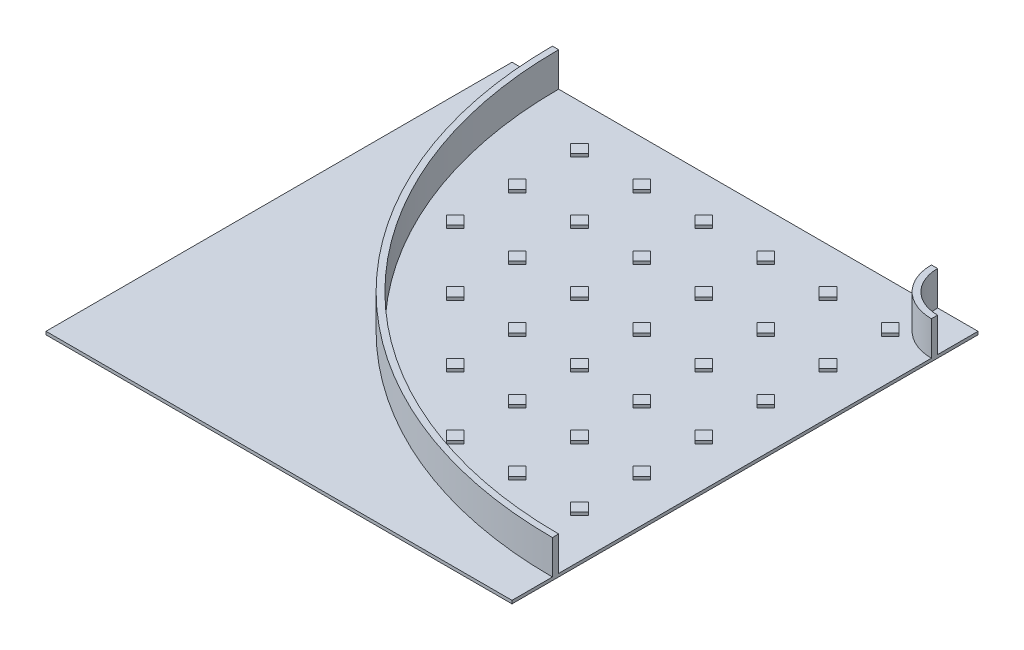
SolidWorks part; units mm, degrees
ref_plane "Front Plane" through (0, 0, 0) normal (0, 0, 1) x (1, 0, 0)
ref_plane "Top Plane" through (0, 0, 0) normal (0, 1, 0) x (1, 0, 0)
ref_plane "Right Plane" through (0, 0, 0) normal (1, 0, 0) x (0, 0, -1)
sketch "Sketch2" plane through (0, 0, 0) normal (0, 1, 0) x (1, 0, 0)
  line L1 (-750, 750) -> (750, 750)
  line L2 (-750, 750) -> (-750, -750)
  line L3 (-750, -750) -> (750, -750)
  line L4 (750, 750) -> (750, -750)
  line L5 (-750, 750) -> (750, -750) construction
  line L6 (-750, -750) -> (750, 750) construction
  point P0 (0, 0)
  dimension "D1" = 1500
  dimension "D2" = 1500
extrude "Boss-Extrude1" add sketch "Sketch2" along normal blind 10
sketch "Sketch3" plane through (0, 10, 0) normal (0, 1, 0) x (1, 0, 0)
  line L0 (620, 750) -> (620, -750) construction
  line L1 (750, 750) -> (-750, 750) construction
  line L2 (-750, -750) -> (750, -750) construction
  line L3 (600, 750) -> (600, -750) construction
  line L4 (750, -750) -> (750, 750) construction
  line L5 (-750, -600) -> (750, -600) construction
  line L6 (-750, 750) -> (-750, -750) construction
  line L7 (-750, -620) -> (750, -620) construction
  line L8 (-750, 0) -> (750, 0) construction
  line L9 (0, 750) -> (0, -750) construction
  line L10 (-750, 620) -> (750, 620) construction
  line L11 (-750, 600) -> (750, 600) construction
  line L12 (-620, 750) -> (-620, -750) construction
  line L13 (-600, 750) -> (-600, -750) construction
  circle A0 centre (750, 750) radius 150
  circle A1 centre (750, 750) radius 1350
  circle A2 centre (750, 750) radius 130
  circle A3 centre (750, 750) radius 1370
  line M3 (750, -750) -> (750, 750)
  line M4 (750, 750) -> (-750, 750)
  dimension "D6" = 150
  dimension "D5" = 20
  dimension "D7" = 20
  dimension "D8" = 150
extrude "Boss-Extrude2" add sketch "Sketch3" along normal blind 110 contours A3 A1 M4 M3 | A2 A0 M4 M3
sketch "Sketch4" plane through (0, 10, 0) normal (0, 1, 0) x (1, 0, 0)
  line L0 (-391.4214, 636.8629) -> (-419.7056, 608.5786)
  line L1 (-391.4214, 636.8629) -> (-363.1371, 608.5786)
  line L2 (-419.7056, 608.5786) -> (-391.4214, 580.2944)
  line L3 (-363.1371, 608.5786) -> (-391.4214, 580.2944)
  line L4 (-391.4214, 636.8629) -> (-391.4214, 580.2944) construction
  line L5 (-419.7056, 608.5786) -> (-363.1371, 608.5786) construction
  line L6 (-191.4214, 636.8629) -> (-219.7056, 608.5786)
  line L7 (-191.4214, 636.8629) -> (-163.1371, 608.5786)
  line L8 (-219.7056, 608.5786) -> (-191.4214, 580.2944)
  line L9 (-163.1371, 608.5786) -> (-191.4214, 580.2944)
  line L10 (-191.4214, 636.8629) -> (-191.4214, 580.2944) construction
  line L11 (-219.7056, 608.5786) -> (-163.1371, 608.5786) construction
  line L12 (8.5786, 636.8629) -> (-19.7056, 608.5786)
  line L13 (8.5786, 636.8629) -> (36.8629, 608.5786)
  line L14 (-19.7056, 608.5786) -> (8.5786, 580.2944)
  line L15 (36.8629, 608.5786) -> (8.5786, 580.2944)
  line L16 (8.5786, 636.8629) -> (8.5786, 580.2944) construction
  line L17 (-19.7056, 608.5786) -> (36.8629, 608.5786) construction
  line L18 (208.5786, 636.8629) -> (180.2944, 608.5786)
  line L19 (208.5786, 636.8629) -> (236.8629, 608.5786)
  line L20 (180.2944, 608.5786) -> (208.5786, 580.2944)
  line L21 (236.8629, 608.5786) -> (208.5786, 580.2944)
  line L22 (208.5786, 636.8629) -> (208.5786, 580.2944) construction
  line L23 (180.2944, 608.5786) -> (236.8629, 608.5786) construction
  line L24 (408.5786, 636.8629) -> (380.2944, 608.5786)
  line L25 (408.5786, 636.8629) -> (436.8629, 608.5786)
  line L26 (380.2944, 608.5786) -> (408.5786, 580.2944)
  line L27 (436.8629, 608.5786) -> (408.5786, 580.2944)
  line L28 (408.5786, 636.8629) -> (408.5786, 580.2944) construction
  line L29 (380.2944, 608.5786) -> (436.8629, 608.5786) construction
  line L30 (-191.4214, 436.8629) -> (-219.7056, 408.5786)
  line L31 (-191.4214, 436.8629) -> (-163.1371, 408.5786)
  line L32 (-219.7056, 408.5786) -> (-191.4214, 380.2944)
  line L33 (-163.1371, 408.5786) -> (-191.4214, 380.2944)
  line L34 (-191.4214, 436.8629) -> (-191.4214, 380.2944) construction
  line L35 (-219.7056, 408.5786) -> (-163.1371, 408.5786) construction
  line L36 (8.5786, 436.8629) -> (-19.7056, 408.5786)
  line L37 (8.5786, 436.8629) -> (36.8629, 408.5786)
  line L38 (-19.7056, 408.5786) -> (8.5786, 380.2944)
  line L39 (36.8629, 408.5786) -> (8.5786, 380.2944)
  line L40 (8.5786, 436.8629) -> (8.5786, 380.2944) construction
  line L41 (-19.7056, 408.5786) -> (36.8629, 408.5786) construction
  line L42 (208.5786, 436.8629) -> (180.2944, 408.5786)
  line L43 (208.5786, 436.8629) -> (236.8629, 408.5786)
  line L44 (180.2944, 408.5786) -> (208.5786, 380.2944)
  line L45 (236.8629, 408.5786) -> (208.5786, 380.2944)
  line L46 (208.5786, 436.8629) -> (208.5786, 380.2944) construction
  line L47 (180.2944, 408.5786) -> (236.8629, 408.5786) construction
  line L48 (408.5786, 436.8629) -> (380.2944, 408.5786)
  line L49 (408.5786, 436.8629) -> (436.8629, 408.5786)
  line L50 (380.2944, 408.5786) -> (408.5786, 380.2944)
  line L51 (436.8629, 408.5786) -> (408.5786, 380.2944)
  line L52 (408.5786, 436.8629) -> (408.5786, 380.2944) construction
  line L53 (380.2944, 408.5786) -> (436.8629, 408.5786) construction
  line L54 (-191.4214, 236.8629) -> (-219.7056, 208.5786)
  line L55 (-191.4214, 236.8629) -> (-163.1371, 208.5786)
  line L56 (-219.7056, 208.5786) -> (-191.4214, 180.2944)
  line L57 (-163.1371, 208.5786) -> (-191.4214, 180.2944)
  line L58 (-191.4214, 236.8629) -> (-191.4214, 180.2944) construction
  line L59 (-219.7056, 208.5786) -> (-163.1371, 208.5786) construction
  line L60 (8.5786, 236.8629) -> (-19.7056, 208.5786)
  line L61 (8.5786, 236.8629) -> (36.8629, 208.5786)
  line L62 (-19.7056, 208.5786) -> (8.5786, 180.2944)
  line L63 (36.8629, 208.5786) -> (8.5786, 180.2944)
  line L64 (8.5786, 236.8629) -> (8.5786, 180.2944) construction
  line L65 (-19.7056, 208.5786) -> (36.8629, 208.5786) construction
  line L66 (208.5786, 236.8629) -> (180.2944, 208.5786)
  line L67 (208.5786, 236.8629) -> (236.8629, 208.5786)
  line L68 (180.2944, 208.5786) -> (208.5786, 180.2944)
  line L69 (236.8629, 208.5786) -> (208.5786, 180.2944)
  line L70 (208.5786, 236.8629) -> (208.5786, 180.2944) construction
  line L71 (180.2944, 208.5786) -> (236.8629, 208.5786) construction
  line L72 (408.5786, 236.8629) -> (380.2944, 208.5786)
  line L73 (408.5786, 236.8629) -> (436.8629, 208.5786)
  line L74 (380.2944, 208.5786) -> (408.5786, 180.2944)
  line L75 (436.8629, 208.5786) -> (408.5786, 180.2944)
  line L76 (408.5786, 236.8629) -> (408.5786, 180.2944) construction
  line L77 (380.2944, 208.5786) -> (436.8629, 208.5786) construction
  line L78 (-191.4214, 36.8629) -> (-219.7056, 8.5786)
  line L79 (-191.4214, 36.8629) -> (-163.1371, 8.5786)
  line L80 (-219.7056, 8.5786) -> (-191.4214, -19.7056)
  line L81 (-163.1371, 8.5786) -> (-191.4214, -19.7056)
  line L82 (-191.4214, 36.8629) -> (-191.4214, -19.7056) construction
  line L83 (-219.7056, 8.5786) -> (-163.1371, 8.5786) construction
  line L84 (8.5786, 36.8629) -> (-19.7056, 8.5786)
  line L85 (8.5786, 36.8629) -> (36.8629, 8.5786)
  line L86 (-19.7056, 8.5786) -> (8.5786, -19.7056)
  line L87 (36.8629, 8.5786) -> (8.5786, -19.7056)
  line L88 (8.5786, 36.8629) -> (8.5786, -19.7056) construction
  line L89 (-19.7056, 8.5786) -> (36.8629, 8.5786) construction
  line L90 (208.5786, 36.8629) -> (180.2944, 8.5786)
  line L91 (208.5786, 36.8629) -> (236.8629, 8.5786)
  line L92 (180.2944, 8.5786) -> (208.5786, -19.7056)
  line L93 (236.8629, 8.5786) -> (208.5786, -19.7056)
  line L94 (208.5786, 36.8629) -> (208.5786, -19.7056) construction
  line L95 (180.2944, 8.5786) -> (236.8629, 8.5786) construction
  line L96 (408.5786, 36.8629) -> (380.2944, 8.5786)
  line L97 (408.5786, 36.8629) -> (436.8629, 8.5786)
  line L98 (380.2944, 8.5786) -> (408.5786, -19.7056)
  line L99 (436.8629, 8.5786) -> (408.5786, -19.7056)
  line L100 (408.5786, 36.8629) -> (408.5786, -19.7056) construction
  line L101 (380.2944, 8.5786) -> (436.8629, 8.5786) construction
  line L102 (750, 750) -> (-750, -750) construction
  line L103 (-391.4214, 636.8629) -> (-191.4214, 636.8629) construction
  line L104 (-419.7056, 608.5786) -> (-419.7056, 408.5786) construction
  line L108 (8.5786, -163.1371) -> (-19.7056, -191.4214)
  line L109 (8.5786, -163.1371) -> (36.8629, -191.4214)
  line L110 (-19.7056, -191.4214) -> (8.5786, -219.7056)
  line L111 (36.8629, -191.4214) -> (8.5786, -219.7056)
  line L112 (8.5786, -163.1371) -> (8.5786, -219.7056) construction
  line L113 (-19.7056, -191.4214) -> (36.8629, -191.4214) construction
  line L114 (208.5786, -163.1371) -> (180.2944, -191.4214)
  line L115 (208.5786, -163.1371) -> (236.8629, -191.4214)
  line L116 (180.2944, -191.4214) -> (208.5786, -219.7056)
  line L117 (236.8629, -191.4214) -> (208.5786, -219.7056)
  line L118 (208.5786, -163.1371) -> (208.5786, -219.7056) construction
  line L119 (180.2944, -191.4214) -> (236.8629, -191.4214) construction
  line L120 (408.5786, -163.1371) -> (380.2944, -191.4214)
  line L121 (408.5786, -163.1371) -> (436.8629, -191.4214)
  line L122 (380.2944, -191.4214) -> (408.5786, -219.7056)
  line L123 (436.8629, -191.4214) -> (408.5786, -219.7056)
  line L124 (408.5786, -163.1371) -> (408.5786, -219.7056) construction
  line L125 (380.2944, -191.4214) -> (436.8629, -191.4214) construction
  line L126 (-391.4214, 436.8629) -> (-419.7056, 408.5786)
  line L127 (-391.4214, 436.8629) -> (-363.1371, 408.5786)
  line L128 (-419.7056, 408.5786) -> (-391.4214, 380.2944)
  line L129 (-363.1371, 408.5786) -> (-391.4214, 380.2944)
  line L130 (-391.4214, 436.8629) -> (-391.4214, 380.2944) construction
  line L131 (-419.7056, 408.5786) -> (-363.1371, 408.5786) construction
  line L132 (-391.4214, 236.8629) -> (-419.7056, 208.5786)
  line L133 (-391.4214, 236.8629) -> (-363.1371, 208.5786)
  line L134 (-419.7056, 208.5786) -> (-391.4214, 180.2944)
  line L135 (-363.1371, 208.5786) -> (-391.4214, 180.2944)
  line L136 (-391.4214, 236.8629) -> (-391.4214, 180.2944) construction
  line L137 (-419.7056, 208.5786) -> (-363.1371, 208.5786) construction
  line L168 (208.5786, -363.1371) -> (180.2944, -391.4214)
  line L169 (208.5786, -363.1371) -> (236.8629, -391.4214)
  line L170 (180.2944, -391.4214) -> (208.5786, -419.7056)
  line L171 (236.8629, -391.4214) -> (208.5786, -419.7056)
  line L172 (208.5786, -363.1371) -> (208.5786, -419.7056) construction
  line L173 (180.2944, -391.4214) -> (236.8629, -391.4214) construction
  line L174 (408.5786, -363.1371) -> (380.2944, -391.4214)
  line L175 (408.5786, -363.1371) -> (436.8629, -391.4214)
  line L176 (380.2944, -391.4214) -> (408.5786, -419.7056)
  line L177 (436.8629, -391.4214) -> (408.5786, -419.7056)
  line L178 (408.5786, -363.1371) -> (408.5786, -419.7056) construction
  line L179 (380.2944, -391.4214) -> (436.8629, -391.4214) construction
  line L180 (608.5786, 636.8629) -> (580.2944, 608.5786)
  line L181 (608.5786, 636.8629) -> (636.8629, 608.5786)
  line L182 (580.2944, 608.5786) -> (608.5786, 580.2944)
  line L183 (636.8629, 608.5786) -> (608.5786, 580.2944)
  line L184 (608.5786, 636.8629) -> (608.5786, 580.2944) construction
  line L185 (580.2944, 608.5786) -> (636.8629, 608.5786) construction
  line L186 (608.5786, 436.8629) -> (580.2944, 408.5786)
  line L187 (608.5786, 436.8629) -> (636.8629, 408.5786)
  line L188 (580.2944, 408.5786) -> (608.5786, 380.2944)
  line L189 (636.8629, 408.5786) -> (608.5786, 380.2944)
  line L190 (608.5786, 436.8629) -> (608.5786, 380.2944) construction
  line L191 (580.2944, 408.5786) -> (636.8629, 408.5786) construction
  line L192 (608.5786, 236.8629) -> (580.2944, 208.5786)
  line L193 (608.5786, 236.8629) -> (636.8629, 208.5786)
  line L194 (580.2944, 208.5786) -> (608.5786, 180.2944)
  line L195 (636.8629, 208.5786) -> (608.5786, 180.2944)
  line L196 (608.5786, 236.8629) -> (608.5786, 180.2944) construction
  line L197 (580.2944, 208.5786) -> (636.8629, 208.5786) construction
  line L198 (608.5786, 36.8629) -> (580.2944, 8.5786)
  line L199 (608.5786, 36.8629) -> (636.8629, 8.5786)
  line L200 (580.2944, 8.5786) -> (608.5786, -19.7056)
  line L201 (636.8629, 8.5786) -> (608.5786, -19.7056)
  line L202 (608.5786, 36.8629) -> (608.5786, -19.7056) construction
  line L203 (580.2944, 8.5786) -> (636.8629, 8.5786) construction
  line L204 (608.5786, -163.1371) -> (580.2944, -191.4214)
  line L205 (608.5786, -163.1371) -> (636.8629, -191.4214)
  line L206 (580.2944, -191.4214) -> (608.5786, -219.7056)
  line L207 (636.8629, -191.4214) -> (608.5786, -219.7056)
  line L208 (608.5786, -163.1371) -> (608.5786, -219.7056) construction
  line L209 (580.2944, -191.4214) -> (636.8629, -191.4214) construction
  line L210 (608.5786, -363.1371) -> (580.2944, -391.4214)
  line L211 (608.5786, -363.1371) -> (636.8629, -391.4214)
  line L212 (580.2944, -391.4214) -> (608.5786, -419.7056)
  line L213 (636.8629, -391.4214) -> (608.5786, -419.7056)
  line L214 (608.5786, -363.1371) -> (608.5786, -419.7056) construction
  line L215 (580.2944, -391.4214) -> (636.8629, -391.4214) construction
  line L216 (-191.4214, -163.1371) -> (-219.7056, -191.4214) [skipped]
  line L217 (-191.4214, -163.1371) -> (-163.1371, -191.4214) [skipped]
  line L218 (-219.7056, -191.4214) -> (-191.4214, -219.7056) [skipped]
  line L219 (-163.1371, -191.4214) -> (-191.4214, -219.7056) [skipped]
  line L220 (-191.4214, -163.1371) -> (-191.4214, -219.7056) construction
  line L221 (-219.7056, -191.4214) -> (-163.1371, -191.4214) construction
  line L222 (-191.4214, -363.1371) -> (-219.7056, -391.4214) [skipped]
  line L223 (-191.4214, -363.1371) -> (-163.1371, -391.4214) [skipped]
  line L224 (-219.7056, -391.4214) -> (-191.4214, -419.7056) [skipped]
  line L225 (-163.1371, -391.4214) -> (-191.4214, -419.7056) [skipped]
  line L226 (-191.4214, -363.1371) -> (-191.4214, -419.7056) construction
  line L227 (-219.7056, -391.4214) -> (-163.1371, -391.4214) construction
  line L228 (8.5786, -363.1371) -> (-19.7056, -391.4214) [skipped]
  line L229 (8.5786, -363.1371) -> (36.8629, -391.4214) [skipped]
  line L230 (-19.7056, -391.4214) -> (8.5786, -419.7056) [skipped]
  line L231 (36.8629, -391.4214) -> (8.5786, -419.7056) [skipped]
  line L232 (8.5786, -363.1371) -> (8.5786, -419.7056) construction
  line L233 (-19.7056, -391.4214) -> (36.8629, -391.4214) construction
  line L234 (-419.7056, -391.4214) -> (-363.1371, -391.4214) construction
  line L235 (-391.4214, 36.8629) -> (-419.7056, 8.5786) [skipped]
  line L236 (-391.4214, 36.8629) -> (-363.1371, 8.5786) [skipped]
  line L237 (-419.7056, 8.5786) -> (-391.4214, -19.7056) [skipped]
  line L238 (-363.1371, 8.5786) -> (-391.4214, -19.7056) [skipped]
  line L239 (-391.4214, 36.8629) -> (-391.4214, -19.7056) construction
  line L240 (-419.7056, 8.5786) -> (-363.1371, 8.5786) construction
  line L241 (-391.4214, -163.1371) -> (-419.7056, -191.4214) [skipped]
  line L242 (-391.4214, -163.1371) -> (-363.1371, -191.4214) [skipped]
  line L243 (-419.7056, -191.4214) -> (-391.4214, -219.7056) [skipped]
  line L244 (-363.1371, -191.4214) -> (-391.4214, -219.7056) [skipped]
  line L245 (-391.4214, -163.1371) -> (-391.4214, -219.7056) construction
  line L246 (-419.7056, -191.4214) -> (-363.1371, -191.4214) construction
  line L247 (-391.4214, -363.1371) -> (-419.7056, -391.4214) [skipped]
  line L248 (-391.4214, -363.1371) -> (-363.1371, -391.4214) [skipped]
  line L249 (-419.7056, -391.4214) -> (-391.4214, -419.7056) [skipped]
  line L250 (-363.1371, -391.4214) -> (-391.4214, -419.7056) [skipped]
  line L251 (-391.4214, -363.1371) -> (-391.4214, -419.7056) construction
  point P1 (-391.4214, 608.5786)
  point P3 (-191.4214, 608.5786)
  point P12 (8.5786, 608.5786)
  point P17 (208.5786, 608.5786)
  point P22 (408.5786, 608.5786)
  point P27 (-191.4214, 408.5786)
  point P32 (8.5786, 408.5786)
  point P37 (208.5786, 408.5786)
  point P42 (408.5786, 408.5786)
  point P47 (-191.4214, 208.5786)
  point P52 (8.5786, 208.5786)
  point P57 (208.5786, 208.5786)
  point P62 (408.5786, 208.5786)
  point P67 (-191.4214, 8.5786)
  point P72 (8.5786, 8.5786)
  point P77 (208.5786, 8.5786)
  point P82 (408.5786, 8.5786)
  point P87 (-191.4214, -391.4214)
  point P88 (8.5786, -391.4214)
  point P90 (-391.4214, 8.5786)
  point P91 (-391.4214, -191.4214)
  point P92 (8.5786, -191.4214)
  point P97 (208.5786, -191.4214)
  point P102 (408.5786, -191.4214)
  point P107 (-391.4214, 408.5786)
  point P112 (-391.4214, 208.5786)
  point P117 (-391.4214, -391.4214)
  point P143 (208.5786, -391.4214)
  point P148 (408.5786, -391.4214)
  point P153 (608.5786, 608.5786)
  point P158 (608.5786, 408.5786)
  point P163 (608.5786, 208.5786)
  point P168 (608.5786, 8.5786)
  point P173 (608.5786, -191.4214)
  point P178 (608.5786, -391.4214)
  point P183 (-191.4214, -191.4214)
  dimension "D1" = 40
  dimension "D2" = 40
  dimension "D5" = 200
  dimension "D6" = 200
  dimension "D7" = 200
  dimension "D3" = 6
  dimension "D4" = 6
extrude "Boss-Extrude3" add sketch "Sketch4" along normal blind 10
equation "\"CellSize\"=1500"
equation "\"D1@Sketch2\"=\"CellSize\""
equation "\"D2@Sketch2\"=\"CellSize\""
equation "\"TrackWidth\"= 1200"
equation "\"C\"=342.079"
equation "\"WallWidth\"=20"
equation "\"D6@Sketch3\"=\"EdgeWidth\""
equation "\"D5@Sketch3\"=\"WallWidth\""
equation "\"D7@Sketch3\"=\"WallWidth\""
equation "\"EdgeWidth\"= ( \"CellSize\" - \"TrackWidth\" ) / 2"
equation "\"D8@Sketch3\"=\"EdgeWidth\""
equation "\"ExtrusionWidth\"=40"
equation "\"D1@Sketch4\"=\"ExtrusionWidth\""
equation "\"D2@Sketch4\"=\"ExtrusionWidth\""
